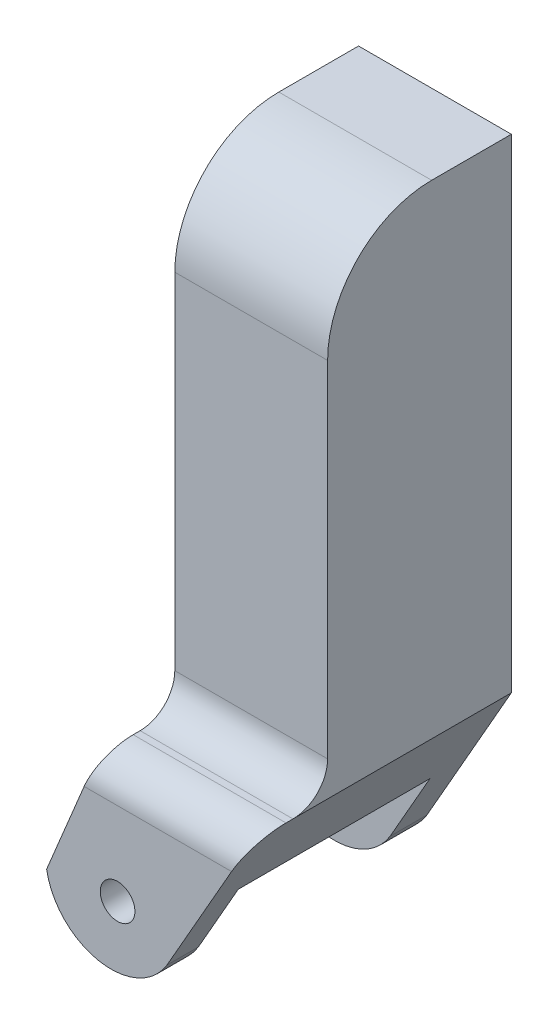
SolidWorks part; units mm, degrees
ref_plane "Спереди" through (0, 0, 0) normal (0, 0, 1) x (1, 0, 0)
ref_plane "Сверху" through (0, 0, 0) normal (0, 1, 0) x (1, 0, 0)
ref_plane "Справа" through (0, 0, 0) normal (1, 0, 0) x (0, 0, -1)
sketch "Эскиз1" plane through (0, 0, 0) normal (0, 0, 1) x (1, 0, 0)
  line L0 (7.5802, -59.7992) -> (-16.7915, -102.5273)
  line L1 (-36.4972, 79.7323) -> (7.5802, 79.7323)
  line L2 (-36.4972, 79.7323) -> (-36.4972, -59.7992)
  line L4 (7.5802, 79.7323) -> (7.5802, -59.7992)
  line L5 (-36.4972, -59.7992) -> (-51.4655, -95.8699)
  arc A0 (-51.4655, -95.8699) -> (-16.7915, -102.5273) centre (-32.8849, -92.7217) ccw
extrude "Бобышка-Вытянуть1" add sketch "Эскиз1" along normal blind 53
sketch "Эскиз2" plane through (0, 0, 53) normal (0, 0, 1) x (1, 0, 0)
  line L0 (-36.4972, -59.7992) -> (7.5802, -59.7992)
  line L5 (-36.4972, 79.7323) -> (-36.4972, -59.7992)
  line L6 (-36.4972, -59.7992) -> (-51.4655, -95.8699)
  line L7 (-16.7915, -102.5273) -> (7.5802, -59.7992)
  line L8 (7.5802, -59.7992) -> (7.5802, 79.7323)
  line L9 (7.5802, 79.7323) -> (-36.4972, 79.7323)
  line L10 (-36.4972, 79.7323) -> (-36.4972, -59.7992)
  line L11 (-36.4972, -59.7992) -> (-51.4655, -95.8699)
  line L12 (-16.7915, -102.5273) -> (7.5802, -59.7992)
  line L13 (7.5802, -59.7992) -> (7.5802, 79.7323)
  line L14 (7.5802, 79.7323) -> (-36.4972, 79.7323)
  arc A1 (-51.4655, -95.8699) -> (-16.7915, -102.5273) centre (-32.8849, -92.7217) ccw
  arc A2 (-51.4655, -95.8699) -> (-16.7915, -102.5273) centre (-32.8849, -92.7217) ccw
  line M8 (-36.4972, -59.7992) -> (-51.4655, -95.8699)
  arc M9 (-51.4655, -95.8699) -> (-16.7915, -102.5273) centre (-32.8849, -92.7217) ccw
  line M10 (-16.7915, -102.5273) -> (7.5802, -59.7992)
  dimension "D1" = 0
extrude "Бобышка-Вытянуть2" add sketch "Эскиз2" along normal blind 22 contours L0 M8 M9 M10
fillet "Скругление2" radius 10 1 edges at (-14.4585, -59.7992, 53)
fillet "Скругление3" radius 10 1 edges at (-14.4585, -59.7992, 75)
sketch "Эскиз3" plane through (-9.9661, 4.1356, 0) normal (-0.9236, 0.3833, 0) x (0, 0, 1)
  line L1 (10.6228, -78.0784) -> (65.9272, -78.0784)
  line L2 (10.6228, -78.0784) -> (10.6228, -139.9734)
  line L3 (10.6228, -139.9734) -> (65.9272, -139.9734)
  line L4 (65.9272, -78.0784) -> (65.9272, -139.9734)
extrude "Вырез-Вытянуть1" cut sketch "Эскиз3" against normal blind 56
sketch "Эскиз4" plane through (0, 0, 75) normal (0, 0, 1) x (1, 0, 0)
  circle A0 centre (-31.0074, -93.6984) radius 5
extrude "Вырез-Вытянуть2" cut sketch "Эскиз4" against normal up to surface (75 mm away) up to face at (-21.4001, -28.4269, 0)
sketch "Эскиз5" plane through (0, 0, 0) normal (0, 0, -1) x (-1, 0, 0)
  circle A0 centre (15.1734, 61.1316) radius 5
extrude "Вырез-Вытянуть3" cut sketch "Эскиз5" against normal blind 10
fillet "Скругление4" radius 30 1 edges at (-14.4585, 79.7323, 53)
